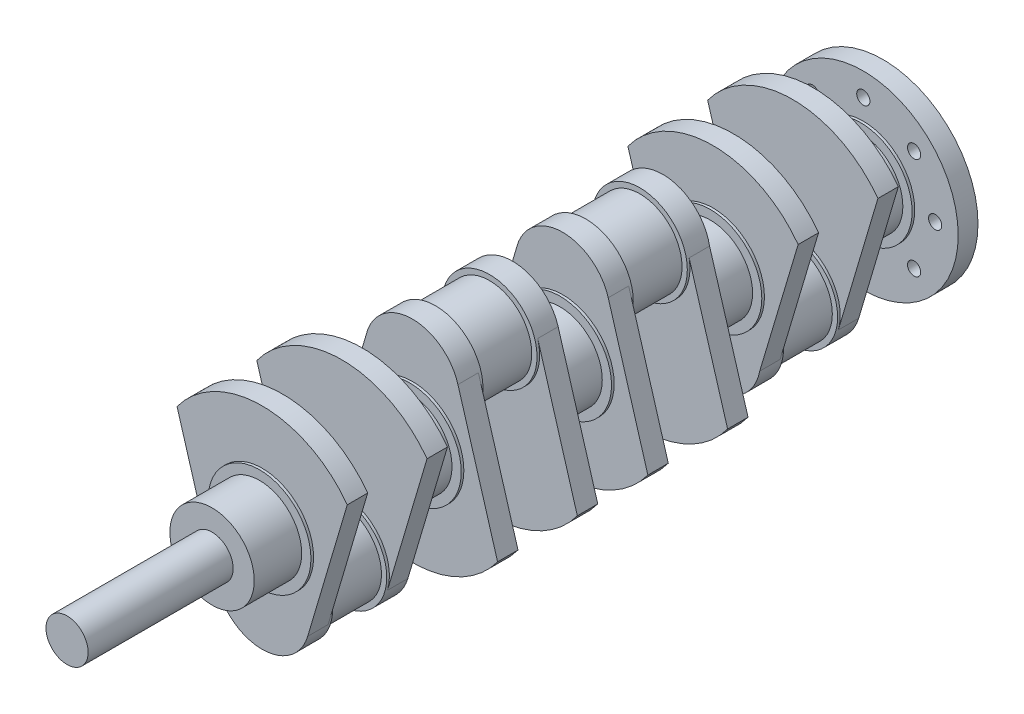
SolidWorks part; units mm, degrees
ref_plane "Front Plane" through (0, 0, 0) normal (0, 0, 1) x (1, 0, 0)
ref_plane "Top Plane" through (0, 0, 0) normal (0, 1, 0) x (1, 0, 0)
ref_plane "Right Plane" through (0, 0, 0) normal (1, 0, 0) x (0, 0, -1)
sketch "Sketch1" plane through (0, 0, 0) normal (0, 0, 1) x (1, 0, 0)
  circle A0 centre (0, 0) radius 72
  circle A2 centre (0, 0) radius 54.5 construction
  circle A3 centre (0, 54.5) radius 5
  circle A4 centre (38.5373, 38.5373) radius 5
  circle A5 centre (54.5, 0) radius 5
  circle A6 centre (38.5373, -38.5373) radius 5
  circle A7 centre (0, -54.5) radius 5
  circle A8 centre (-38.5373, -38.5373) radius 5
  circle A9 centre (-54.5, 0) radius 5
  circle A10 centre (-38.5373, 38.5373) radius 5
  point P23 (0, 0)
  dimension "D1" = 144
  dimension "D2" = 8
extrude "Boss-Extrude1" add sketch "Sketch1" along normal blind 15
sketch "Sketch2" plane through (0, 0, 15) normal (0, 0, 1) x (1, 0, 0)
  circle A0 centre (0, 0) radius 39
extrude "Boss-Extrude2" add sketch "Sketch2" along normal blind 2
sketch "Sketch3" plane through (0, 0, 17) normal (0, 0, 1) x (1, 0, 0)
  circle A0 centre (0, 0) radius 32
extrude "Boss-Extrude3" add sketch "Sketch3" along normal blind 36 contours A0
sketch "Sketch4" plane through (0, 0, 53) normal (0, 0, 1) x (1, 0, 0)
  circle A0 centre (0, 0) radius 80
extrude "Boss-Extrude4" add sketch "Sketch4" along normal blind 15.5
sketch "Sketch5" plane through (0, 0, 68.5) normal (0, 0, 1) x (1, 0, 0)
  line L0 (0, 0) -> (0, -89.6994) construction
  line L1 (0, 0) -> (0, 83.3159) construction
  line L2 (-34.5175, -54.2246) -> (-64.5699, 47.2306)
  line L3 (34.5175, -54.2246) -> (64.5699, 47.2306)
  circle A0 centre (0, -44) radius 36
  circle A1 centre (0, 0) radius 80 construction
  arc A2 (-64.5699, 47.2306) -> (64.5699, 47.2306) centre (0, 0) ccw
  circle M6 centre (0, 0) radius 80
  dimension "D1" = 44
  dimension "D4" = 72
  dimension "D2" = 33
  dimension "D3" = 16.5
extrude "Cut-Extrude2" cut sketch "Sketch5" against normal blind 15.5 contours A0 L2 M6 | A0 L3 M6
sketch "Sketch7" plane through (0, 0, 53) normal (0, 0, -1) x (-1, 0, 0)
  circle A0 centre (0, 0) radius 32
  circle A1 centre (0, 0) radius 39
extrude "Boss-Extrude6" add sketch "Sketch7" along normal blind 2
sketch "Sketch9" plane through (0, 0, 68.5) normal (0, 0, 1) x (1, 0, 0)
  circle A0 centre (0, -44) radius 36
extrude "Boss-Extrude7" add sketch "Sketch9" along normal blind 2
sketch "Sketch10" plane through (0, 0, 70.5) normal (0, 0, 1) x (1, 0, 0)
  circle A0 centre (0, -44) radius 32
extrude "Boss-Extrude8" add sketch "Sketch10" along normal blind 41
sketch "Sketch11" plane through (0, 0, 111.5) normal (0, 0, 1) x (1, 0, 0)
  circle A0 centre (0, -44) radius 36
extrude "Boss-Extrude9" add sketch "Sketch11" along normal blind 2
sketch "Sketch13" plane through (0, 0, 113.5) normal (0, 0, 1) x (1, 0, 0)
  line L0 (-64.5699, 47.2306) -> (-35.1039, -51.9823)
  line L1 (64.5699, 47.2306) -> (35.3889, -50.6052)
  arc A0 (-35.1039, -51.9823) -> (35.3889, -50.6052) centre (0, -44) ccw
  arc A1 (64.5699, 47.2306) -> (-64.5699, 47.2306) centre (0, 0) ccw
extrude "Boss-Extrude10" add sketch "Sketch13" along normal blind 15.5
sketch "Sketch14" plane through (0, 0, 129) normal (0, 0, 1) x (1, 0, 0)
  circle A0 centre (0, 0) radius 39
extrude "Boss-Extrude11" add sketch "Sketch14" along normal blind 2
sketch "Sketch15" plane through (0, 0, 131) normal (0, 0, 1) x (1, 0, 0)
  circle A0 centre (0, 0) radius 32
extrude "Boss-Extrude12" add sketch "Sketch15" along normal blind 34
sketch "Sketch16" plane through (0, 0, 165) normal (0, 0, 1) x (1, 0, 0)
  circle A0 centre (0, 0) radius 39
extrude "Boss-Extrude13" add sketch "Sketch16" along normal blind 2
sketch "Sketch17" plane through (0, 0, 167) normal (0, 0, 1) x (1, 0, 0)
  line L4 (-96.193, 0) -> (141.0977, 0) construction
  line L5 (-64.5699, -47.2306) -> (-35.1039, 51.9823)
  line L6 (64.5699, -47.2306) -> (35.3889, 50.6052)
  arc A2 (64.5699, -47.2306) -> (-64.5699, -47.2306) centre (0, 0) cw
  arc A3 (-35.1039, 51.9823) -> (35.3889, 50.6052) centre (0, 44) cw
extrude "Boss-Extrude14" add sketch "Sketch17" along normal blind 15.5
sketch "Sketch18" plane through (0, 0, 182.5) normal (0, 0, 1) x (1, 0, 0)
  circle A0 centre (0, 44) radius 36
extrude "Boss-Extrude15" add sketch "Sketch18" along normal blind 2
sketch "Sketch19" plane through (0, 0, 184.5) normal (0, 0, 1) x (1, 0, 0)
  circle A0 centre (0, 44) radius 32
extrude "Boss-Extrude16" add sketch "Sketch19" along normal blind 41
sketch "Sketch20" plane through (0, 0, 225.5) normal (0, 0, 1) x (1, 0, 0)
  circle A0 centre (0, 44) radius 36
extrude "Boss-Extrude17" add sketch "Sketch20" along normal blind 2
sketch "Sketch21" plane through (0, 0, 227.5) normal (0, 0, 1) x (1, 0, 0)
  line L0 (-64.5699, -47.2306) -> (-34.9429, 52.6599)
  line L1 (64.5699, -47.2306) -> (34.5175, 54.2246)
  arc A0 (34.5175, 54.2246) -> (-34.9429, 52.6599) centre (0, 44) ccw
  arc A1 (-64.5699, -47.2306) -> (0, 80) centre (0, 0) ccw
  circle M2 centre (0, 44) radius 36
extrude "Boss-Extrude18" add sketch "Sketch21" along normal blind 15.5 contours L0 A1 L1 M2 | A0 M2
sketch "Sketch22" plane through (0, 0, 243) normal (0, 0, 1) x (1, 0, 0)
  circle A0 centre (0, 0) radius 39
extrude "Boss-Extrude19" add sketch "Sketch22" along normal blind 2
sketch "Sketch23" plane through (0, 0, 245) normal (0, 0, 1) x (1, 0, 0)
  circle A0 centre (0, 0) radius 32
extrude "Boss-Extrude20" add sketch "Sketch23" along normal blind 34
sketch "Sketch24" plane through (0, 0, 279) normal (0, 0, 1) x (1, 0, 0)
  circle A0 centre (0, 0) radius 39
extrude "Boss-Extrude21" add sketch "Sketch24" along normal blind 2
sketch "Sketch25" plane through (0, 0, 281) normal (0, 0, 1) x (1, 0, 0)
  line L2 (-110.9789, 0) -> (108.4819, 0) construction
  line L5 (64.5699, -47.2306) -> (34.5175, 54.2246)
  line L6 (-64.5699, -47.2306) -> (-34.5175, 54.2246)
  arc A4 (-64.5699, -47.2306) -> (64.5699, -47.2306) centre (0, 0) ccw
  arc A5 (34.5175, 54.2246) -> (-34.5175, 54.2246) centre (0, 44) ccw
extrude "Boss-Extrude22" add sketch "Sketch25" along normal blind 15.5
sketch "Sketch29" plane through (0, 0, 296.5) normal (0, 0, 1) x (1, 0, 0)
  circle A0 centre (0, 44) radius 36
extrude "Boss-Extrude26" add sketch "Sketch29" along normal blind 2
sketch "Sketch30" plane through (0, 0, 298.5) normal (0, 0, 1) x (1, 0, 0)
  circle A0 centre (0, 44) radius 32
extrude "Boss-Extrude27" add sketch "Sketch30" along normal blind 41
sketch "Sketch31" plane through (0, 0, 339.5) normal (0, 0, 1) x (1, 0, 0)
  circle A1 centre (0, 44) radius 36
extrude "Boss-Extrude28" add sketch "Sketch31" along normal blind 2
sketch "Sketch32" plane through (0, 0, 341.5) normal (0, 0, 1) x (1, 0, 0)
  line L0 (-64.5699, -47.2306) -> (-33.9298, 56.0319)
  line L1 (64.5699, -47.2306) -> (34.5175, 54.2246)
  arc A0 (34.5175, 54.2246) -> (-35.0012, 52.4213) centre (0, 44) ccw
  arc A1 (-64.5699, -47.2306) -> (64.5699, -47.2306) centre (0, 0) ccw
  circle M1 centre (0, 44) radius 36
extrude "Boss-Extrude29" add sketch "Sketch32" along normal blind 15.5 contours L0 A1 L1 M1 | L0 M1
sketch "Sketch33" plane through (0, 0, 357) normal (0, 0, 1) x (1, 0, 0)
  circle A0 centre (0, 0) radius 39
extrude "Boss-Extrude30" add sketch "Sketch33" along normal blind 2
sketch "Sketch34" plane through (0, 0, 359) normal (0, 0, 1) x (1, 0, 0)
  circle A0 centre (0, 0) radius 32
extrude "Boss-Extrude31" add sketch "Sketch34" along normal blind 34
sketch "Sketch35" plane through (0, 0, 393) normal (0, 0, 1) x (1, 0, 0)
  circle A0 centre (0, 0) radius 39
extrude "Boss-Extrude32" add sketch "Sketch35" along normal blind 2
sketch "Sketch36" plane through (0, 0, 395) normal (0, 0, 1) x (1, 0, 0)
  line L0 (-64.5699, 47.2306) -> (-35.1039, -51.9823)
  line L1 (-64.5699, 47.2306) -> (-35.1039, -51.9823) construction
  line L2 (64.5699, 47.2306) -> (34.5175, -54.2246)
  arc A0 (64.5699, 47.2306) -> (-64.5699, 47.2306) centre (0, 0) ccw
  arc A1 (-35.1039, -51.9823) -> (34.5175, -54.2246) centre (0, -44) ccw
  dimension "D1" = 36
extrude "Boss-Extrude33" add sketch "Sketch36" along normal blind 15.5
sketch "Sketch37" plane through (0, 0, 410.5) normal (0, 0, 1) x (1, 0, 0)
  circle A0 centre (0, -44) radius 36
  point P3 (0, 0)
  dimension "D1" = 72
extrude "Boss-Extrude34" add sketch "Sketch37" along normal blind 2 contours A0
sketch "Sketch38" plane through (0, 0, 412.5) normal (0, 0, 1) x (1, 0, 0)
  circle A0 centre (0, -44) radius 32
extrude "Boss-Extrude35" add sketch "Sketch38" along normal blind 41
sketch "Sketch39" plane through (0, 0, 453.5) normal (0, 0, 1) x (1, 0, 0)
  line L0 (0, 1.7217) -> (0, -8) construction
  line L1 (0, -88) -> (0, 88) construction
  line L3 (-36, -44) -> (-97.8653, -44) construction
  line L4 (0, -80) -> (0, -88.5374) construction
  circle A0 centre (0, -44) radius 36
  dimension "D1" = 72
extrude "Boss-Extrude36" add sketch "Sketch39" along normal blind 2
sketch "Sketch42" plane through (0, 0, 455.5) normal (0, 0, 1) x (1, 0, 0)
  line L0 (-64.5699, 47.2306) -> (-35.1039, -51.9823)
  line L1 (-64.5699, 47.2306) -> (-35.1039, -51.9823) construction
  line L2 (64.5699, 47.2306) -> (34.5175, -54.2246)
  arc A0 (-35.1039, -51.9823) -> (34.5175, -54.2246) centre (0, -44) ccw
  arc A1 (64.5699, 47.2306) -> (-64.5699, 47.2306) centre (0, 0) ccw
extrude "Boss-Extrude37" add sketch "Sketch42" along normal blind 15.5
sketch "Sketch43" plane through (0, 0, 471) normal (0, 0, 1) x (1, 0, 0)
  circle A0 centre (0, 0) radius 39
extrude "Boss-Extrude38" add sketch "Sketch43" along normal blind 2
sketch "Sketch44" plane through (0, 0, 473) normal (0, 0, 1) x (1, 0, 0)
  circle A0 centre (0, 0) radius 32
extrude "Boss-Extrude39" add sketch "Sketch44" along normal blind 36
sketch "Sketch45" plane through (0, 0, 509) normal (0, 0, 1) x (1, 0, 0)
  circle A0 centre (0, 0) radius 16
extrude "Boss-Extrude40" add sketch "Sketch45" along normal blind 110
